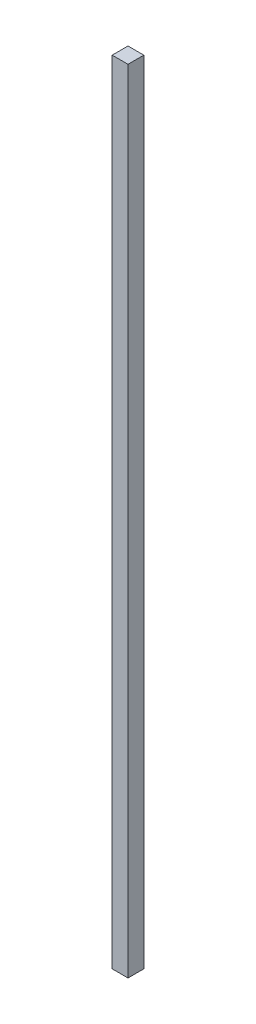
SolidWorks part; units mm, degrees
ref_plane "Front Plane" through (0, 0, 0) normal (0, 0, 1) x (1, 0, 0)
ref_plane "Top Plane" through (0, 0, 0) normal (0, 1, 0) x (1, 0, 0)
ref_plane "Right Plane" through (0, 0, 0) normal (1, 0, 0) x (0, 0, -1)
sketch "Sketch1" plane through (0, 0, 0) normal (0, 1, 0) x (1, 0, 0)
  line L1 (-39.8355, 18.6136) -> (-14.4355, 18.6136)
  line L2 (-39.8355, 18.6136) -> (-39.8355, -6.7864)
  line L3 (-39.8355, -6.7864) -> (-14.4355, -6.7864)
  line L4 (-14.4355, 18.6136) -> (-14.4355, -6.7864)
  dimension "D1" = 25.4
  dimension "D2" = 25.4
extrude "Boss-Extrude1" add sketch "Sketch1" along normal blind 1270
